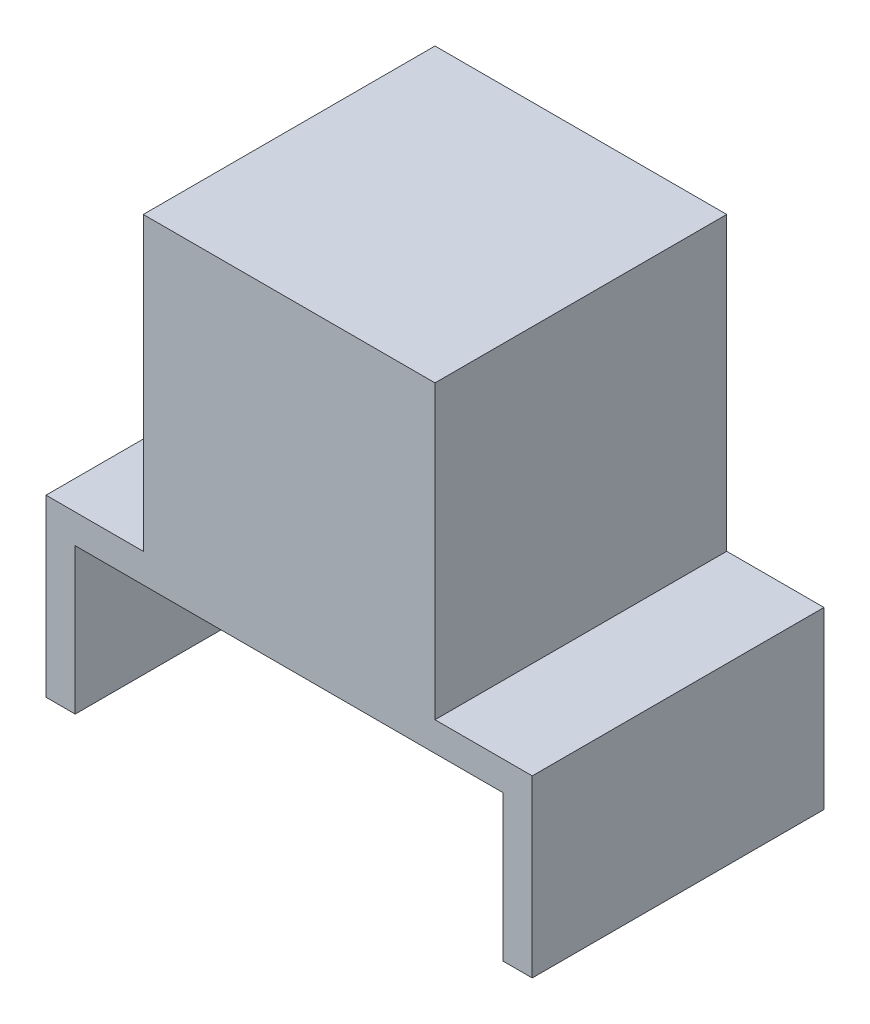
SolidWorks part; units mm, degrees
ref_plane "前视基准面" through (0, 0, 0) normal (0, 0, 1) x (1, 0, 0)
ref_plane "上视基准面" through (0, 0, 0) normal (0, 1, 0) x (1, 0, 0)
ref_plane "右视基准面" through (0, 0, 0) normal (1, 0, 0) x (0, 0, -1)
sketch "草图1" plane through (0, 0, 0) normal (0, 0, 1) x (1, 0, 0)
  line L1 (-8.042, 15.5944) -> (21.958, 15.5944)
  line L2 (-8.042, 15.5944) -> (-8.042, -14.4056)
  line L3 (-8.042, -14.4056) -> (21.958, -14.4056)
  line L4 (21.958, 15.5944) -> (21.958, -14.4056)
  dimension "D1" = 30
  dimension "D2" = 30
extrude "凸台-拉伸1" add sketch "草图1" along normal blind 30
sketch "草图2" plane through (0, -14.4056, 0) normal (0, -1, 0) x (1, 0, 0)
  line L0 (-8.042, 30) -> (-8.042, 0) construction
  line L1 (-18.042, 40) -> (31.958, 40)
  line L2 (-18.042, 40) -> (-18.042, 0)
  line L3 (-18.042, 0) -> (31.958, 0)
  line L4 (31.958, 40) -> (31.958, 0)
  dimension "D1" = 50
  dimension "D2" = 10
extrude "凸台-拉伸2" add sketch "草图2" along normal blind 3
sketch "草图3" plane through (0, -17.4056, 0) normal (0, -1, 0) x (1, 0, 0)
  line L10 (-18.042, 0) -> (31.958, 0) construction
  line L11 (-18.042, 40) -> (-15.042, 40)
  line L12 (-18.042, 40) -> (-18.042, 0)
  line L13 (-18.042, 0) -> (-15.042, 0)
  line L14 (-15.042, 40) -> (-15.042, 0)
  line L15 (31.958, 40) -> (-18.042, 40) construction
  line L16 (31.958, 0) -> (28.958, 0)
  line L17 (31.958, 0) -> (31.958, 40)
  line L18 (31.958, 40) -> (28.958, 40)
  line L19 (28.958, 0) -> (28.958, 40)
  dimension "D1" = 3
  dimension "D2" = 3
extrude "凸台-拉伸3" add sketch "草图3" along normal blind 15
sketch "草图4" plane through (0, -14.4056, 0) normal (0, 1, 0) x (1, 0, 0)
  line L1 (31.958, -40) -> (-18.7868, -40)
  line L2 (31.958, -40) -> (31.958, -30)
  line L3 (31.958, -30) -> (-18.7868, -30)
  line L4 (-18.7868, -40) -> (-18.7868, -30)
extrude "切除-拉伸1" cut sketch "草图4" against normal through all
